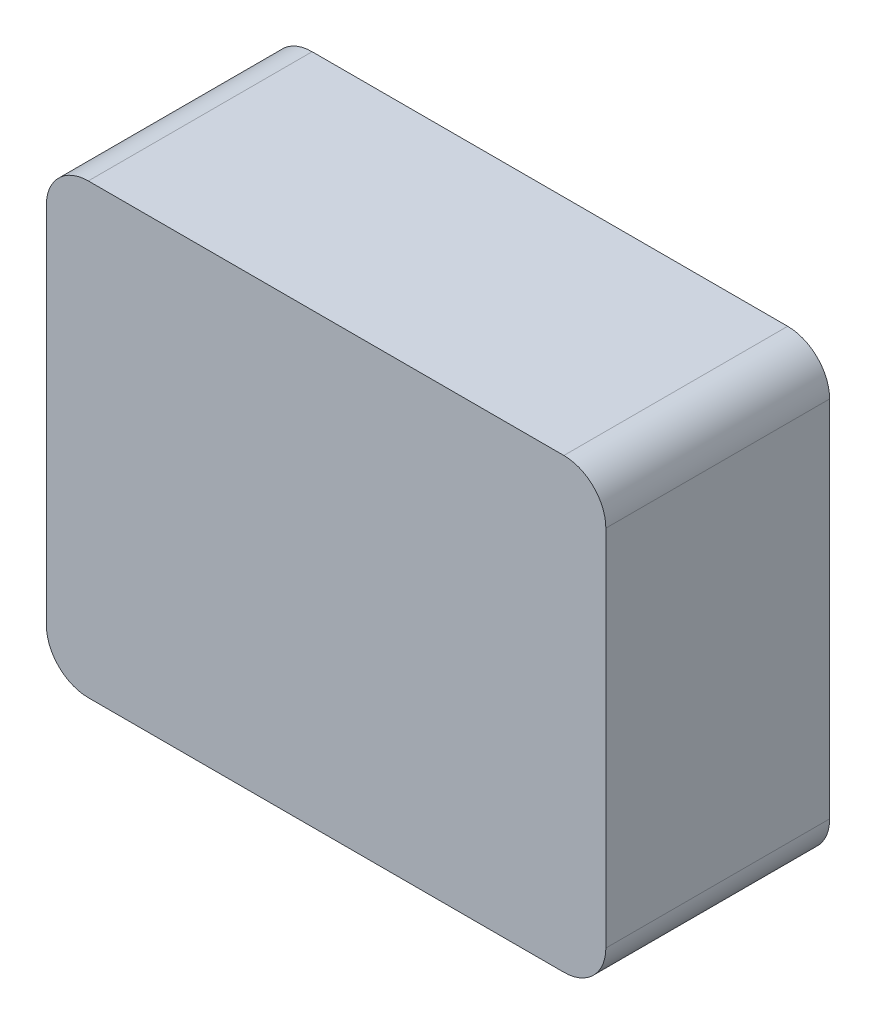
SolidWorks part; units mm, degrees
ref_plane "Front" through (0, 0, 0) normal (0, 0, 1) x (1, 0, 0)
ref_plane "Top" through (0, 0, 0) normal (0, 1, 0) x (1, 0, 0)
ref_plane "Right" through (0, 0, 0) normal (1, 0, 0) x (0, 0, -1)
sketch "Sketch1" plane through (0, 0, 0) normal (0, 0, 1) x (1, 0, 0)
  line L1 (0, 0) -> (127, 0)
  line L2 (0, 0) -> (0, 101.6)
  line L3 (0, 101.6) -> (127, 101.6)
  line L4 (127, 0) -> (127, 101.6)
  dimension "D1" = 127
  dimension "D2" = 101.6
extrude "Extrude1" add sketch "Sketch1" along normal blind 50.8
fillet "Fillet1" radius 9.525
